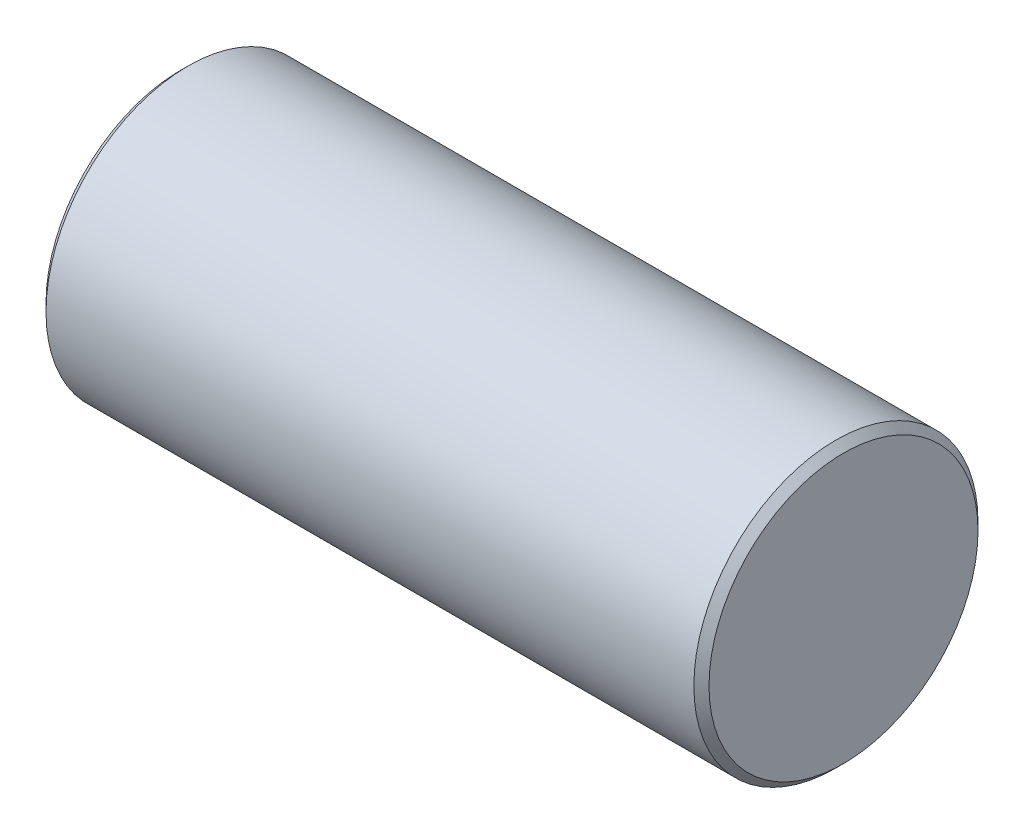
SolidWorks part; units mm, degrees
material "6061-T6 (SS)"
ref_plane "Front Plane" through (0, 0, 0) normal (0, 0, 1) x (1, 0, 0)
ref_plane "Top Plane" through (0, 0, 0) normal (0, 1, 0) x (1, 0, 0)
ref_plane "Right Plane" through (0, 0, 0) normal (1, 0, 0) x (0, 0, -1)
sketch "Sketch1" plane through (0, 0, 0) normal (1, 0, 0) x (0, 0, -1)
  circle A0 centre (0, 0) radius 4.7625
  dimension "D1" = 9.525
extrude "Boss-Extrude1" add sketch "Sketch1" along normal mid plane 22.225
ref_plane "Plane1" through (0, 0, -4.7625) normal (0, 0, -1) x (-1, 0, 0)
sketch "Sketch2" plane through (0, 0, -4.7625) normal (0, 0, -1) x (-1, 0, 0)
  line L0 (11.1125, 4.7625) -> (-11.1125, 4.7625) construction
  line L1 (4.1275, -4.7625) -> (-4.1275, -4.7625)
  line L2 (4.1275, -4.7625) -> (4.1275, 4.7625)
  line L3 (4.1275, 4.7625) -> (-4.1275, 4.7625)
  line L4 (-4.1275, -4.7625) -> (-4.1275, 4.7625)
  line L5 (4.1275, -4.7625) -> (-4.1275, 4.7625) construction
  line L6 (4.1275, 4.7625) -> (-4.1275, -4.7625) construction
  point P0 (0, 0)
  dimension "D1" = 8.255
extrude "Cut-Extrude1" cut sketch "Sketch2" against normal blind 0.508
hole_wizard "#4-40 Tapped Hole1" positions "Sketch4" profile "Sketch5" tap size "#4-40" standard "ANSI Inch"
sketch "Sketch4" plane through (0, 0, -4.2545) normal (0, 0, -1) x (-1, 0, 0)
  point P0 (0, 0)
sketch "Sketch5" plane through (0, 0, -4.2545) normal (1, 0, 0) x (0, 1, 0)
  line L0 (0, 0) -> (0, 4.4892)
  line L1 (0, 4.4892) -> (1.1303, 3.81)
  line L2 (1.1303, 3.81) -> (1.1303, 0)
  line L5 (1.1303, 0) -> (0, 0)
  line L10 (0, 4.4892) -> (-1.1303, 3.81) construction
  line L11 (0, -6.35) -> (0, 107.95) construction
  dimension "Tap Drill Dia." = 2.2606
  dimension "Tap Drill Depth" = 3.81
  dimension "Drill Angle" = 118
cosmetic thread "Hole Thread1" parameters "D1"=2.54, "D2"=2.8448
chamfer "Chamfer1" distance 0.254 angle 45 2 edges at (-11.1125, 0, -4.7625) (11.1125, 0, -4.7625)
